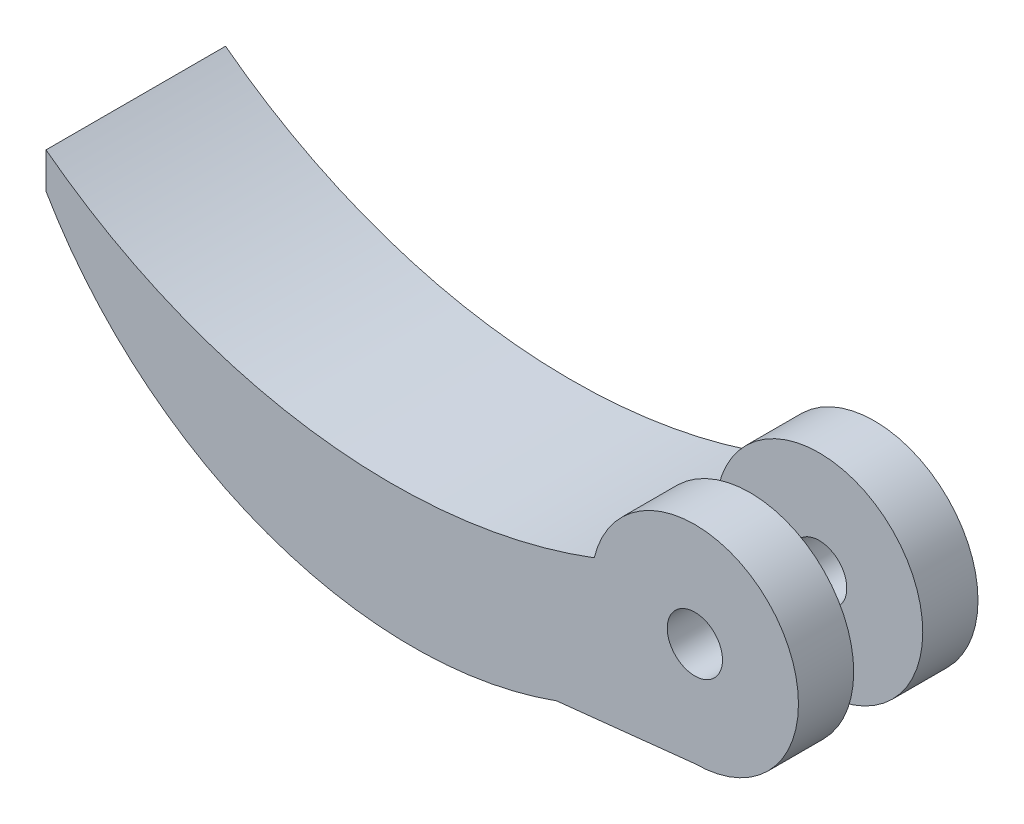
SolidWorks part; units mm, degrees
material "AISI 304"
ref_plane "Alzado" through (0, 0, 0) normal (0, 0, 1) x (1, 0, 0)
ref_plane "Planta" through (0, 0, 0) normal (0, 1, 0) x (1, 0, 0)
ref_plane "Vista lateral" through (0, 0, 0) normal (1, 0, 0) x (0, 0, -1)
sketch "Croquis1" plane through (0, 0, 0) normal (0, 0, 1) x (1, 0, 0)
  circle A0 centre (0, 0) radius 2
  circle A1 centre (0, 0) radius 7.5
  dimension "D1" = 4
  dimension "D2" = 15
extrude "Saliente-Extruir1" add sketch "Croquis1" along normal blind 4
sketch "Croquis2" plane through (0, 0, 0) normal (0, 0, -1) x (-1, 0, 0)
  circle A0 centre (0, 0) radius 2.1938
extrude "Saliente-Extruir2" add sketch "Croquis2" along normal blind 5 separate body
sketch "Croquis3" plane through (0, 0, -5) normal (0, 0, -1) x (-1, 0, 0)
  circle A0 centre (0, 0) radius 2
  circle A1 centre (0, 0) radius 7.5
  dimension "D1" = 4
  dimension "D2" = 15
extrude "Saliente-Extruir3" add sketch "Croquis3" along normal blind 4 separate body
sketch "Croquis4" plane through (0, 0, -5) normal (0, 0, -1) x (-1, 0, 0)
  circle A0 centre (0, 0) radius 2.1938
extrude "Cortar-Extruir1" cut sketch "Croquis4" against normal blind 14
sketch "Croquis5" plane through (0, 0, 4) normal (0, 0, 1) x (1, 0, 0)
  line L2 (-10.0093, -8.5669) -> (0, -7.5)
  line L3 (-46.9818, 4.9039) -> (-46.9818, 7.5)
  circle A0 centre (0, 0) radius 7.5 construction
  arc A1 (-10.0093, -8.5669) -> (-46.9818, 4.9039) centre (-20.4372, 20.2857) cw
  arc A2 (-7.2888, 1.7674) -> (-46.9818, 7.5) centre (-21.9545, 40.5062) cw
  arc A3 (-7.2888, 1.7674) -> (0, -7.5) centre (0, 0) ccw
  point P9 (0, 0)
  point P10 (-7.2888, 1.7674)
extrude "Saliente-Extruir4" add sketch "Croquis5" against normal blind 13
